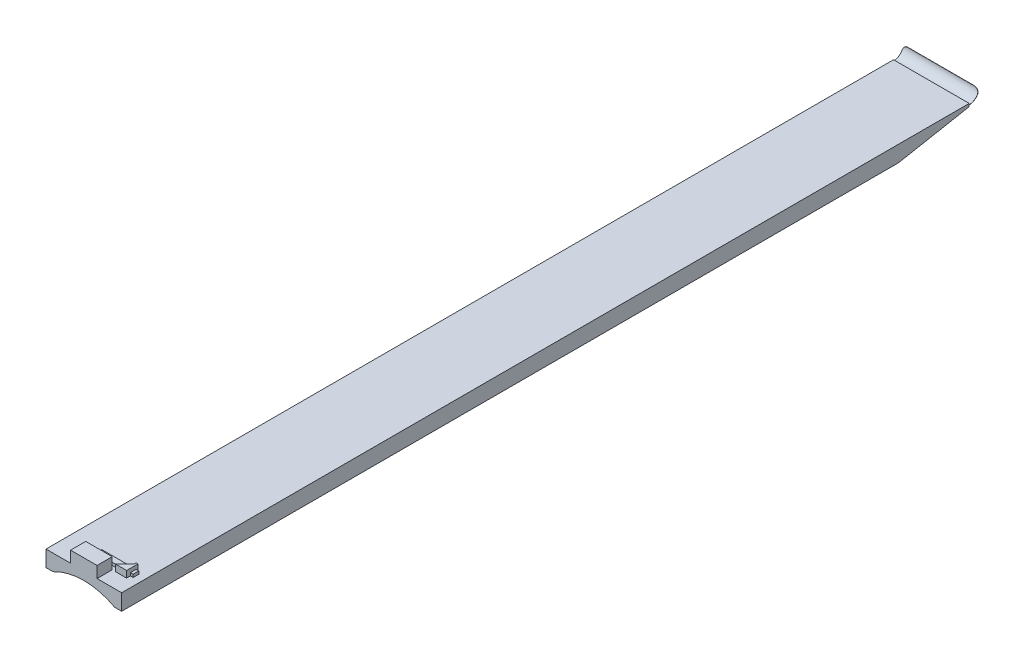
SolidWorks part; units mm, degrees
material "6061-T6 (SS)"
ref_plane "Front Plane" through (0, 0, 0) normal (0, 0, 1) x (1, 0, 0)
ref_plane "Top Plane" through (0, 0, 0) normal (0, 1, 0) x (1, 0, 0)
ref_plane "Right Plane" through (0, 0, 0) normal (1, 0, 0) x (0, 0, -1)
sketch "Sketch3" plane through (0, 0, 0) normal (1, 0, 0) x (0, 0, -1)
  line L0 (2844.8, 44.45) -> (2607.6294, 0)
  line L1 (0, 0) -> (2607.6294, 0)
  line L2 (0, 0) -> (0, 53.975)
  line L3 (0, 53.975) -> (2844.8, 53.975)
  line L4 (2844.8, 49.53) -> (2844.8, 44.45)
  line L5 (2844.8, 53.975) -> (2844.8, 50.165) construction
  line L6 (2844.8, 53.975) -> (2844.8, 93.4026) construction
  line L8 (2876.55, 81.915) -> (2877.185, 81.915)
  line L9 (2844.8, 53.975) -> (2844.8, 50.165)
  arc A0 (2844.8, 50.165) -> (2876.55, 81.915) centre (2844.8, 81.915) ccw
  arc A1 (2844.8, 49.53) -> (2877.185, 81.915) centre (2844.8, 81.915) ccw
  dimension "D6" = 63.5
  dimension "D7" = 64.77
  dimension "D1" = 53.975
  dimension "D2" = 2844.8
  dimension "D3" = 9.525
  dimension "D4" = 241.3
  dimension "D5" = 3.81
extrude "Boss-Extrude1" add sketch "Sketch3" against normal blind 254
sketch "Sketch5" plane through (0, 0, 0) normal (0, 0, 1) x (1, 0, 0)
  line L0 (0, 65.7225) -> (-254, 65.7225) construction
  line L1 (0, 49.53) -> (0, 81.915) construction
  line L2 (-254, 81.915) -> (-254, 49.53) construction
  line L3 (-254, 81.915) -> (0, 81.915) construction
  line L4 (0, 65.7225) -> (0, 81.915)
  line L5 (0, 81.915) -> (-16.1925, 81.915)
  line L6 (-254, 65.7225) -> (-254, 81.915)
  line L7 (-254, 81.915) -> (-237.8075, 81.915)
  arc A0 (0, 65.7225) -> (-16.1925, 81.915) centre (-16.1925, 65.7225) ccw
  arc A1 (-237.8075, 81.915) -> (-254, 65.7225) centre (-237.8075, 65.7225) ccw
  point P8 (0, 65.7225)
extrude "Cut-Extrude1" cut sketch "Sketch5" against normal through all
sketch "Sketch6" plane through (0, 0, 0) normal (0, 0, 1) x (1, 0, 0)
  line L0 (-254, 53.975) -> (0, 53.975) construction
  line L1 (-254, 0) -> (0, 0) construction
  circle A0 centre (-127, -191.7827) radius 217.8177
  point P6 (-127, 0)
  dimension "D1" = 435.6354
  dimension "D2" = 245.7577
extrude "Cut-Extrude2" cut sketch "Sketch6" against normal through all
sketch "Sketch7" plane through (0, 53.975, 0) normal (0, 1, 0) x (1, 0, 0)
  line L0 (-254, 0) -> (0, 0) construction
  line L1 (-171.45, 0) -> (-82.55, 0)
  line L2 (-171.45, 0) -> (-171.45, 50.8)
  line L3 (-171.45, 50.8) -> (-82.55, 50.8)
  line L4 (-82.55, 0) -> (-82.55, 50.8)
  point P6 (-127, 0)
  point P7 (-127, 0)
  dimension "D1" = 88.9
  dimension "D2" = 50.8
extrude "Boss-Extrude2" add sketch "Sketch7" along normal blind 38.1
sketch "Sketch8" plane through (0, 53.975, 0) normal (0, 1, 0) x (1, 0, 0)
  line L0 (-34.2199, 88.9) -> (-34.2199, 82.55)
  line L1 (-148.9009, 63.5) -> (-72.3199, 63.5)
  line L2 (-148.9009, 63.5) -> (-148.9009, 82.55)
  line L3 (-148.9009, 82.55) -> (-40.5699, 82.55)
  line L4 (-25.0759, 63.5) -> (-25.0759, 82.55)
  line L5 (-34.2199, 50.8) -> (-72.3199, 50.8)
  line L6 (-34.2199, 88.9) -> (-40.5699, 88.9)
  line L7 (-40.5699, 88.9) -> (-40.5699, 82.55)
  line L8 (-72.3199, 50.8) -> (-72.3199, 63.5)
  line L9 (-34.2199, 63.5) -> (-25.0759, 63.5)
  line L10 (-34.2199, 63.5) -> (-34.2199, 50.8)
  line L11 (-34.2199, 82.55) -> (-25.0759, 82.55)
  line L12 (-82.55, 0) -> (0, 0) construction
  dimension "D1" = 123.825
  dimension "D2" = 19.05
  dimension "D3" = 9.144
  dimension "D4" = 38.1
  dimension "D5" = 12.7
  dimension "D6" = 6.35
  dimension "D7" = 6.35
  dimension "D8" = 50.8
extrude "Boss-Extrude3" add sketch "Sketch8" along normal blind 9.525
sketch "Sketch9" plane through (0, 63.5, 0) normal (0, 1, 0) x (1, 0, 0)
  line L0 (-72.3199, 50.8) -> (-40.5699, 82.55)
  line L1 (-40.5699, 82.55) -> (-40.5699, 88.9)
  line L2 (-40.5699, 88.9) -> (-34.2199, 88.9)
  line L3 (-34.2199, 88.9) -> (-34.2199, 50.8)
  line L4 (-34.2199, 50.8) -> (-72.3199, 50.8)
extrude "Boss-Extrude4" add sketch "Sketch9" along normal blind 12.7
